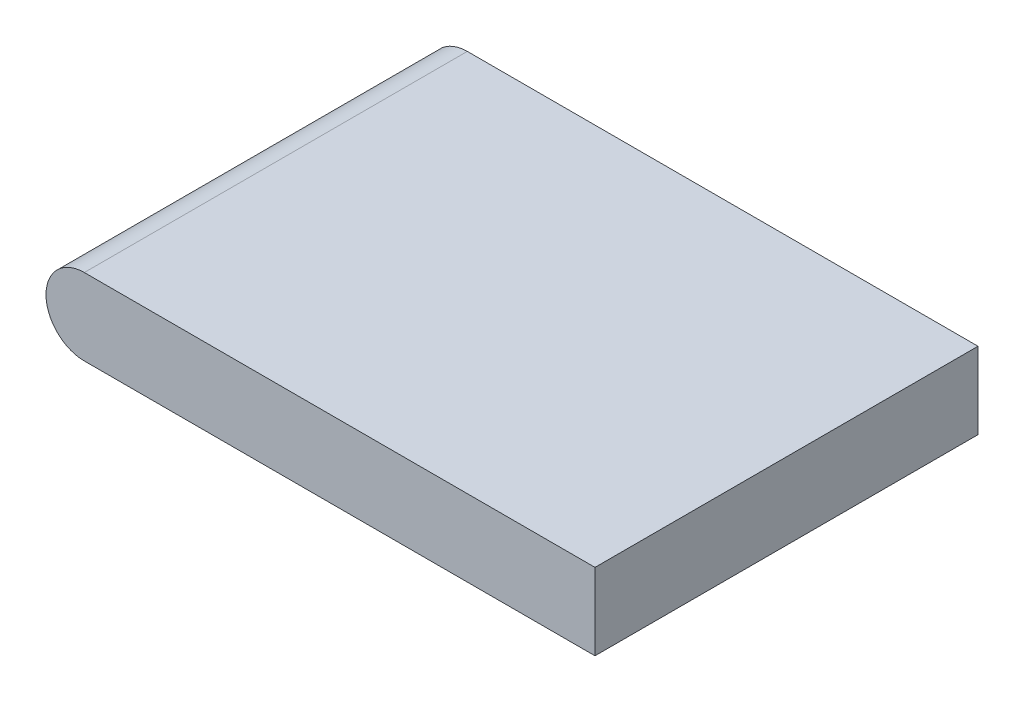
SolidWorks part; units mm, degrees
material "Pure Gold"
ref_plane "Front Plane" through (0, 0, 0) normal (0, 0, 1) x (1, 0, 0)
ref_plane "Top Plane" through (0, 0, 0) normal (0, 1, 0) x (1, 0, 0)
ref_plane "Right Plane" through (0, 0, 0) normal (1, 0, 0) x (0, 0, -1)
sketch "Sketch1" plane through (0, 0, 0) normal (0, 0, 1) x (1, 0, 0)
  line L1 (-12.7, 1.905) -> (12.7, 1.905)
  line L2 (-12.7, 1.905) -> (-12.7, -1.905)
  line L3 (-12.7, -1.905) -> (12.7, -1.905)
  line L4 (12.7, 1.905) -> (12.7, -1.905)
  line L5 (-12.7, 1.905) -> (12.7, -1.905) construction
  line L6 (-12.7, -1.905) -> (12.7, 1.905) construction
  circle A0 centre (-12.7, 0) radius 1.905
  point P0 (0, 0)
  dimension "D3" = 3.81
  dimension "D1" = 25.4
  dimension "D2" = 3.81
extrude "Boss-Extrude1" add sketch "Sketch1" along normal mid plane 19.05 contours A0 L3 L4 L1 | L2 A0 | L2 A0
